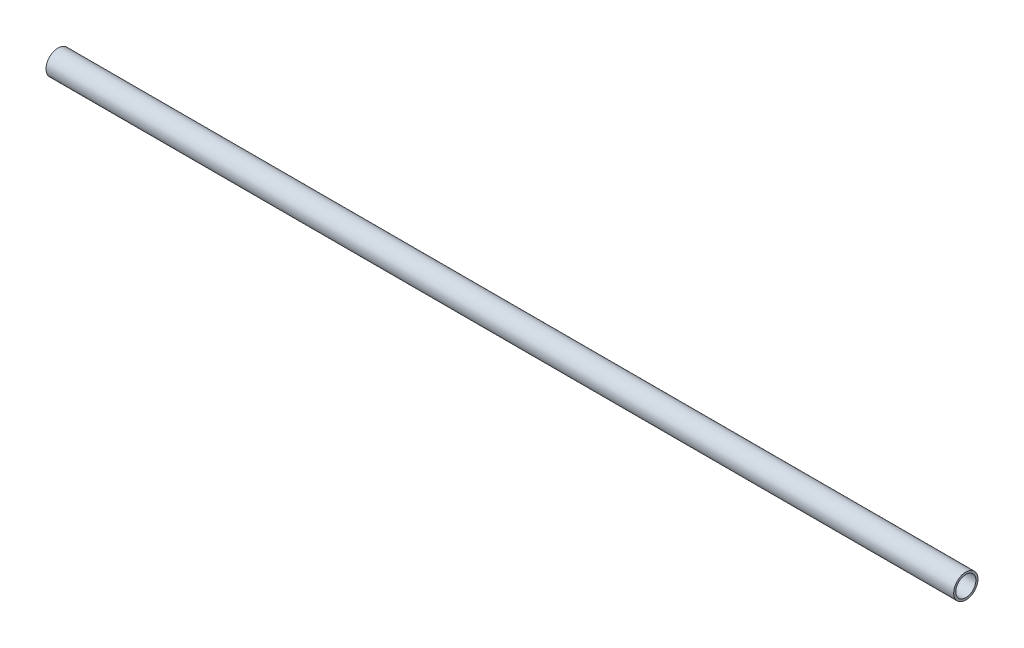
SolidWorks part; units mm, degrees
material "6061 Alloy"
ref_plane "Front Plane" through (0, 0, 0) normal (0, 0, 1) x (1, 0, 0)
ref_plane "Top Plane" through (0, 0, 0) normal (0, 1, 0) x (1, 0, 0)
ref_plane "Right Plane" through (0, 0, 0) normal (1, 0, 0) x (0, 0, -1)
sketch "Sketch1" plane through (0, 0, 0) normal (1, 0, 0) x (0, 0, -1)
  circle A0 centre (0, 0) radius 9.525
  circle A1 centre (0, 0) radius 7.874
  dimension "D1" = 19.05
  dimension "D2" = 15.748
extrude "Boss-Extrude1" add sketch "Sketch1" along normal mid plane 711.2
